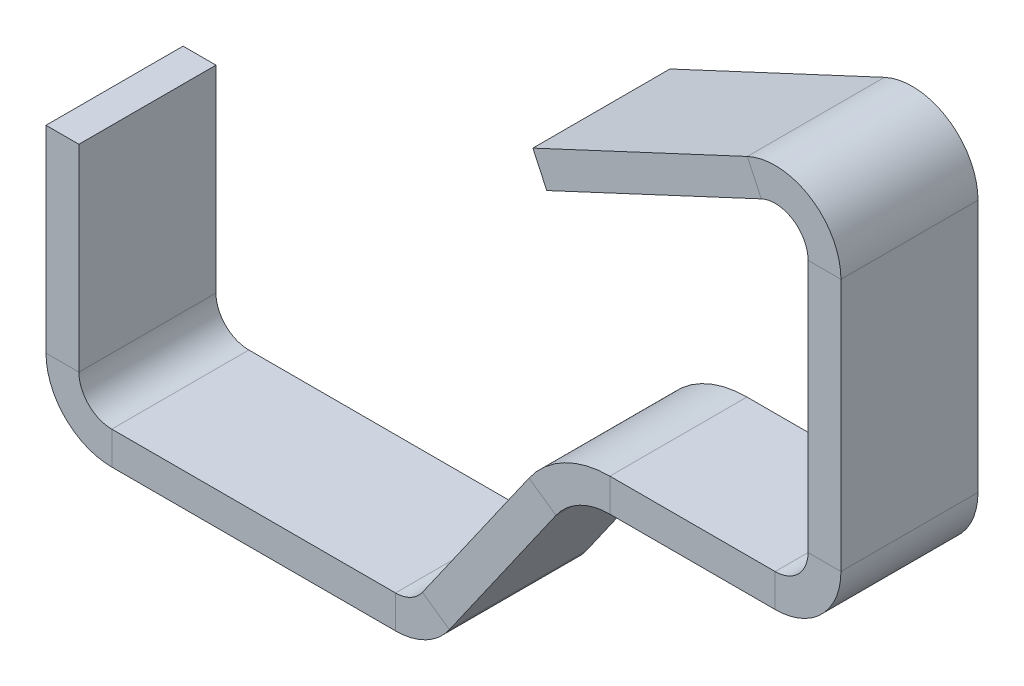
SolidWorks part; units mm, degrees
ref_plane "Front Plane" through (0, 0, 0) normal (0, 0, 1) x (1, 0, 0)
ref_plane "Top Plane" through (0, 0, 0) normal (0, 1, 0) x (1, 0, 0)
ref_plane "Right Plane" through (0, 0, 0) normal (1, 0, 0) x (0, 0, -1)
sketch "Sketch1" plane through (0, 0, 0) normal (0, 0, 1) x (1, 0, 0)
  line L0 (0, 0) -> (0, -36)
  line L1 (12, -48) -> (63.7532, -48)
  line L2 (73.583, -42.8829) -> (93.0249, -15.1171)
  line L3 (102.8547, -10) -> (133, -10)
  line L4 (145, 2) -> (145, 48.1638)
  line L5 (127.9286, 59.0395) -> (88.8089, 40.7977)
  arc A0 (145, 48.1638) -> (127.9286, 59.0395) centre (133, 48.1638) ccw
  arc A1 (133, -10) -> (145, 2) centre (133, 2) ccw
  arc A2 (93.0249, -15.1171) -> (102.8547, -10) centre (102.8547, -22) cw
  arc A3 (63.7532, -48) -> (73.583, -42.8829) centre (63.7532, -36) ccw
  arc A4 (0, -36) -> (12, -48) centre (12, -36) ccw
  point P7 (0, 0)
  point P8 (0, 0)
  point P9 (0, 0)
  point P10 (0, 0)
  point P11 (0, 0)
  point P14 (145, 67)
  point P17 (145, -10)
  point P23 (70, -48)
  point P26 (0, -48)
  dimension "D1" = 48
  dimension "D9" = 12
  dimension "D2" = 145
  dimension "D3" = 75
  dimension "D4" = 38
  dimension "D5" = 115
  dimension "D6" = 62
  dimension "D7" = 55
  dimension "D8" = 115
ref_plane "Plane1" through (0, 0, 0) normal (0, -1, 0) x (-1, 0, 0)
sketch "Sketch2" plane through (0, 0, 0) normal (0, -1, 0) x (-1, 0, 0)
  line L0 (-12, 0) -> (-63.7532, 0) construction
  line L1 (-6, 12.5) -> (0, 12.5)
  line L2 (-6, 12.5) -> (-6, -12.5)
  line L3 (-6, -12.5) -> (0, -12.5)
  line L4 (0, 12.5) -> (0, -12.5)
  line L5 (-6, 12.5) -> (0, -12.5) construction
  line L6 (-6, -12.5) -> (0, 12.5) construction
  point P0 (-3, 0)
  dimension "D1" = 6
  dimension "D2" = 25
sweep "Sweep1" add profiles "Sketch2" path "Sketch1"
